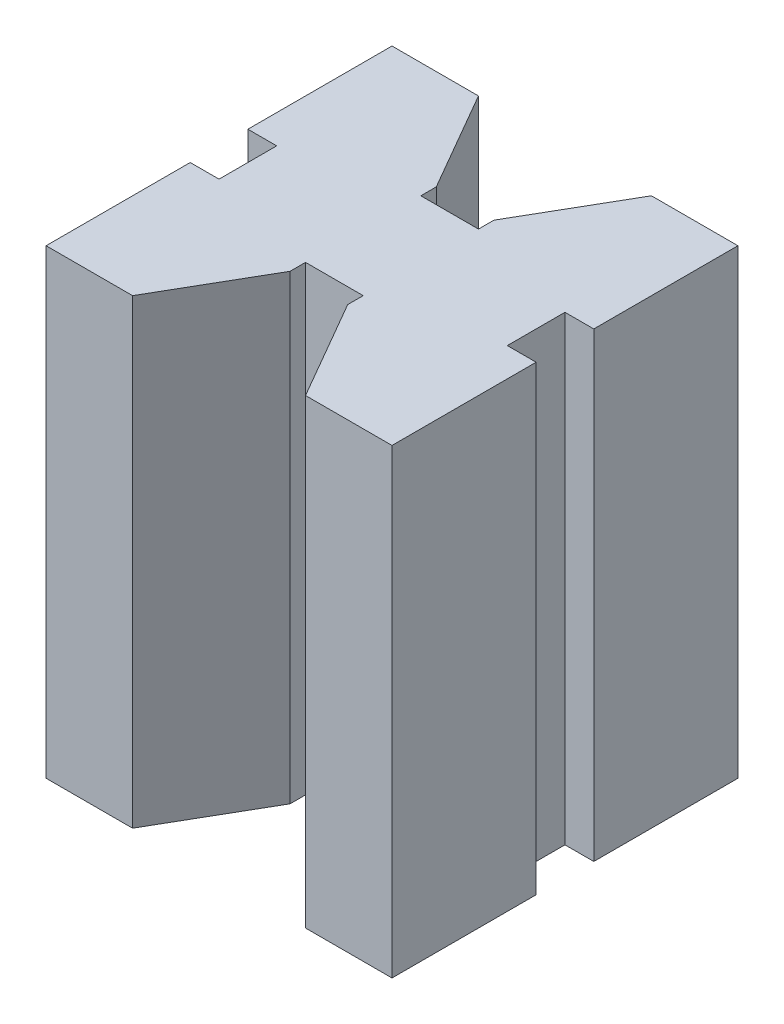
SolidWorks part; units mm, degrees
material "1060 Alloy"
ref_plane "Front Plane" through (0, 0, 0) normal (0, 0, 1) x (1, 0, 0)
ref_plane "Top Plane" through (0, 0, 0) normal (0, 1, 0) x (1, 0, 0)
ref_plane "Right Plane" through (0, 0, 0) normal (1, 0, 0) x (0, 0, -1)
sketch "Sketch1" plane through (0, 0, 0) normal (0, 1, 0) x (1, 0, 0)
  line L0 (-30, 17.5) -> (-27.5, 17.5)
  line L1 (0, 0) -> (-7.5, 0)
  line L2 (0, 0) -> (0, 12.5)
  line L3 (0, 30) -> (-7.5, 30)
  line L4 (-30, 0) -> (-30, 12.5)
  line L5 (-27.5, 17.5) -> (-27.5, 12.5)
  line L6 (-27.5, 12.5) -> (-30, 12.5)
  line L7 (0, 17.5) -> (-2.5, 17.5)
  line L8 (-2.5, 17.5) -> (-2.5, 12.5)
  line L9 (-2.5, 12.5) -> (0, 12.5)
  line L10 (-30, 17.5) -> (-30, 30)
  line L11 (0, 17.5) -> (0, 30)
  line L12 (-22.5, 30) -> (-17.5, 21.3397)
  line L14 (-12.5, 21.3397) -> (-7.5, 30)
  line L15 (-22.5, 0) -> (-17.5, 8.6603)
  line L17 (-12.5, 8.6603) -> (-7.5, 0)
  line L18 (-22.5, 30) -> (-30, 30)
  line L19 (-22.5, 0) -> (-30, 0)
  line L20 (-17.5, 21.3397) -> (-17.5, 20)
  line L21 (-17.5, 20) -> (-12.5, 20)
  line L22 (-12.5, 20) -> (-12.5, 21.3397)
  line L23 (-17.5, 8.6603) -> (-17.5, 10)
  line L24 (-17.5, 10) -> (-12.5, 10)
  line L25 (-12.5, 10) -> (-12.5, 8.6603)
  point P19 (-15, 20)
  point P26 (-15, 10)
  dimension "D1" = 30
  dimension "D2" = 30
  dimension "D3" = 5
  dimension "D4" = 5
  dimension "D5" = 12.5
  dimension "D6" = 25
  dimension "D7" = 2.5
  dimension "D8" = 15
  dimension "D9" = 15
  dimension "D10" = 5
  dimension "D11" = 5
  dimension "D12" = 15
  dimension "D13" = 15
  dimension "D14" = 7.5
  dimension "D15" = 7.5
  dimension "D16" = 240
  dimension "D17" = 240
  dimension "D18" = 240
  dimension "D19" = 240
  dimension "D20" = 10
  dimension "D21" = 10
extrude "Boss-Extrude1" add sketch "Sketch1" along normal blind 40
sketch "Sketch2" plane through (0, 0, 0) normal (1, 0, 0) x (0, 0, -1)
  line L0 (17.5, 40) -> (17.5, 0) construction
  line L1 (12.5, 40) -> (17.5, 40) construction
  circle A0 centre (15, 20) radius 2.5
  dimension "D2" = 5
  dimension "D1" = 2.5
  dimension "D3" = 20
sketch "Sketch4" plane through (0, 0, 0) normal (0, 0, 1) x (1, 0, 0)
  line L0 (-17.5, 0) -> (-12.5, 0) construction
  line L1 (-12.5, 40) -> (-12.5, 0) construction
  circle A0 centre (-15, 20) radius 2.5
  dimension "D2" = 5
  dimension "D1" = 20
  dimension "D3" = 2.5
sketch "Sketch5" plane through (0, 0, 0) normal (0, 1, 0) x (1, 0, 0)
